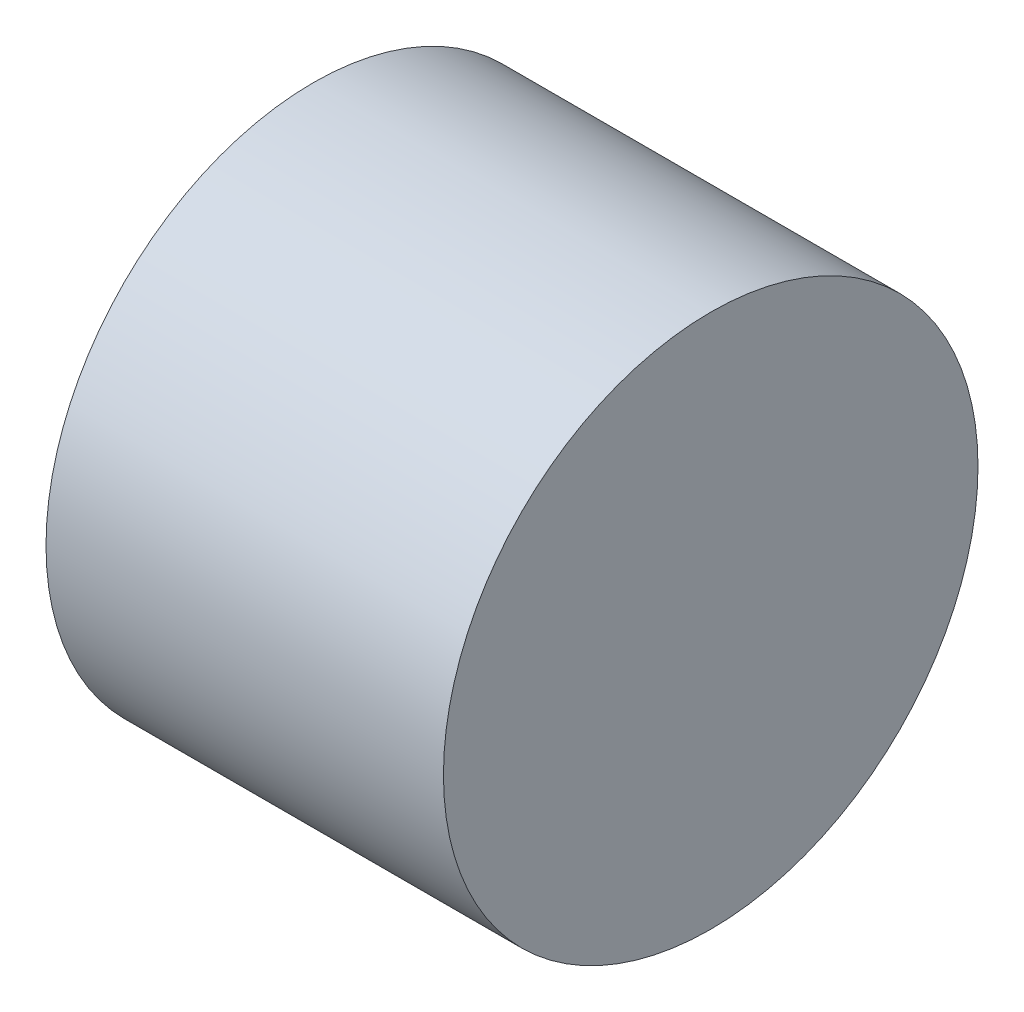
SolidWorks part; units mm, degrees
ref_plane "Front Plane" through (0, 0, 0) normal (0, 0, 1) x (1, 0, 0)
ref_plane "Top Plane" through (0, 0, 0) normal (0, 1, 0) x (1, 0, 0)
ref_plane "Right Plane" through (0, 0, 0) normal (1, 0, 0) x (0, 0, -1)
sketch "Sketch1" plane through (0, 0, 0) normal (1, 0, 0) x (0, 0, -1)
  circle A0 centre (0, 0) radius 6.725
  dimension "D1" = 13.45
extrude "Boss-Extrude1" add sketch "Sketch1" against normal blind 10 contours A0
